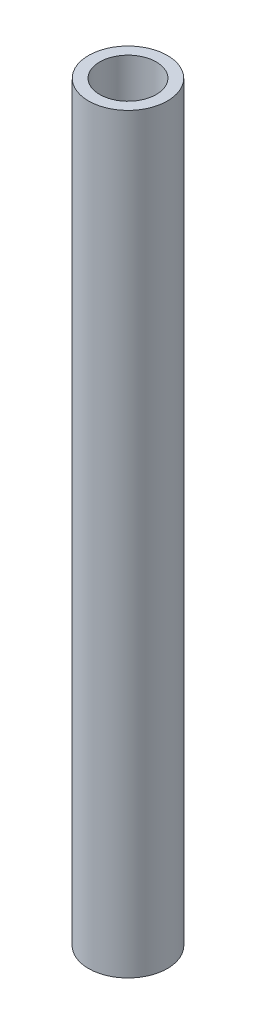
SolidWorks part; units mm, degrees
ref_plane "Front Plane" through (0, 0, 0) normal (0, 0, 1) x (1, 0, 0)
ref_plane "Top Plane" through (0, 0, 0) normal (0, 1, 0) x (1, 0, 0)
ref_plane "Right Plane" through (0, 0, 0) normal (1, 0, 0) x (0, 0, -1)
sketch "Sketch1" plane through (0, 0, 0) normal (0, 1, 0) x (1, 0, 0)
  circle A0 centre (0, 0) radius 10.668
  circle A1 centre (0, 0) radius 7.6454
  dimension "D1" = 21.336
  dimension "D2" = 15.2908
extrude "Boss-Extrude1" add sketch "Sketch1" along normal blind 203.2
ref_plane "Plane1" through (0, 101.6, 0) normal (0, -1, 0) x (-1, 0, 0)
